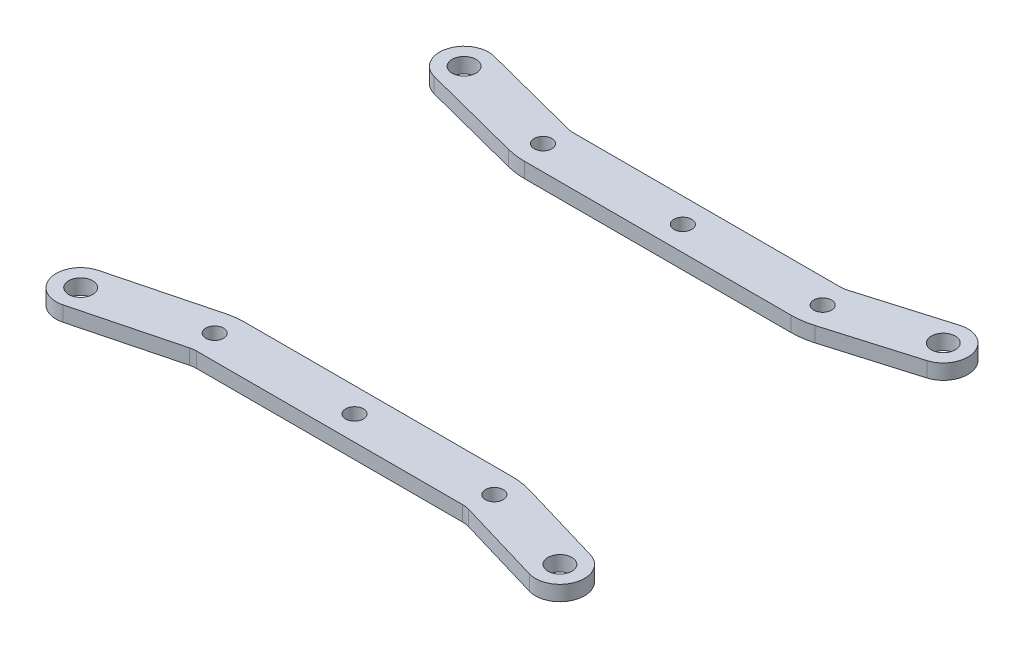
SolidWorks part; units mm, degrees
ref_plane "Front Plane" through (0, 0, 0) normal (0, 0, 1) x (1, 0, 0)
ref_plane "Top Plane" through (0, 0, 0) normal (0, 1, 0) x (1, 0, 0)
ref_plane "Right Plane" through (0, 0, 0) normal (1, 0, 0) x (0, 0, -1)
sketch "Sketch1" plane through (0, 0, 0) normal (0, 1, 0) x (1, 0, 0)
  line L0 (0, 25.4) -> (0, 0) construction
  line L1 (0, 0) -> (25.4, 0) construction
  circle A0 centre (0, 0) radius 3.175
  circle A1 centre (25.4, 0) radius 3.175
  circle A2 centre (50.8, 0) radius 3.175
  circle A3 centre (76.2, 0) radius 3.175
  circle A4 centre (101.6, 0) radius 3.175
  circle A5 centre (127, 0) radius 3.175
  circle A6 centre (152.4, 0) radius 3.175
  circle A7 centre (25.4, 25.4) radius 3.175
  circle A8 centre (50.8, 25.4) radius 3.175
  circle A9 centre (76.2, 25.4) radius 3.175
  circle A10 centre (101.6, 25.4) radius 3.175
  circle A11 centre (127, 25.4) radius 3.175
  circle A12 centre (152.4, 25.4) radius 3.175
  circle A13 centre (25.4, 50.8) radius 3.175
  circle A14 centre (50.8, 50.8) radius 3.175
  circle A15 centre (76.2, 50.8) radius 3.175
  circle A16 centre (101.6, 50.8) radius 3.175
  circle A17 centre (127, 50.8) radius 3.175
  circle A18 centre (152.4, 50.8) radius 3.175
  circle A19 centre (25.4, 76.2) radius 3.175
  circle A20 centre (50.8, 76.2) radius 3.175
  circle A21 centre (76.2, 76.2) radius 3.175
  circle A22 centre (101.6, 76.2) radius 3.175
  circle A23 centre (127, 76.2) radius 3.175
  circle A24 centre (152.4, 76.2) radius 3.175
  circle A25 centre (25.4, 101.6) radius 3.175
  circle A26 centre (50.8, 101.6) radius 3.175
  circle A27 centre (76.2, 101.6) radius 3.175
  circle A28 centre (101.6, 101.6) radius 3.175
  circle A29 centre (127, 101.6) radius 3.175
  circle A30 centre (152.4, 101.6) radius 3.175
  circle A31 centre (25.4, 127) radius 3.175
  circle A32 centre (50.8, 127) radius 3.175
  circle A33 centre (76.2, 127) radius 3.175
  circle A34 centre (101.6, 127) radius 3.175
  circle A35 centre (127, 127) radius 3.175
  circle A36 centre (152.4, 127) radius 3.175
  circle A37 centre (25.4, 152.4) radius 3.175
  circle A38 centre (50.8, 152.4) radius 3.175
  circle A39 centre (76.2, 152.4) radius 3.175
  circle A40 centre (101.6, 152.4) radius 3.175
  circle A41 centre (127, 152.4) radius 3.175
  circle A42 centre (152.4, 152.4) radius 3.175
  circle A43 centre (0, 25.4) radius 3.175
  circle A44 centre (0, 50.8) radius 3.175
  circle A45 centre (0, 76.2) radius 3.175
  circle A46 centre (0, 101.6) radius 3.175
  circle A47 centre (0, 127) radius 3.175
  circle A48 centre (0, 152.4) radius 3.175
  dimension "D1" = 6.35
  dimension "D4" = 25.4
  dimension "D2" = 7
  dimension "D3" = 7
sketch "Sketch2" plane through (0, 0, 0) normal (0, 1, 0) x (1, 0, 0)
  line L0 (25.975, 2.3) -> (25.975, 7.3)
  line L1 (12.925, 99.3) -> (25.975, 99.3)
  line L2 (12.925, 99.3) -> (12.925, 2.3)
  line L3 (12.925, 2.3) -> (25.975, 2.3)
  line L4 (39.975, 99.3) -> (39.975, 2.3)
  line L5 (30.475, 7.3) -> (30.475, 2.3)
  line L6 (25.975, 99.3) -> (25.975, 94.3)
  line L7 (30.475, 94.3) -> (30.475, 99.3)
  line L8 (30.475, 99.3) -> (39.975, 99.3)
  line L9 (30.475, 2.3) -> (39.975, 2.3)
  line L10 (49.975, 99.3) -> (49.975, 2.3)
  line L11 (49.975, 2.3) -> (63.025, 2.3)
  line L12 (63.025, 2.3) -> (63.025, 7.3)
  line L13 (67.525, 7.3) -> (67.525, 2.3)
  line L14 (67.525, 2.3) -> (77.025, 2.3)
  line L15 (77.025, 99.3) -> (77.025, 2.3)
  line L16 (67.525, 99.3) -> (77.025, 99.3)
  line L17 (67.525, 94.3) -> (67.525, 99.3)
  line L18 (63.025, 99.3) -> (63.025, 94.3)
  line L19 (49.975, 99.3) -> (63.025, 99.3)
  line L20 (87.025, 99.3) -> (87.025, 2.3)
  line L21 (87.025, 2.3) -> (100.075, 2.3)
  line L22 (100.075, 2.3) -> (100.075, 7.3)
  line L23 (104.575, 7.3) -> (104.575, 2.3)
  line L24 (104.575, 2.3) -> (114.075, 2.3)
  line L25 (114.075, 99.3) -> (114.075, 2.3)
  line L26 (104.575, 99.3) -> (114.075, 99.3)
  line L27 (104.575, 94.3) -> (104.575, 99.3)
  line L28 (100.075, 99.3) -> (100.075, 94.3)
  line L29 (87.025, 99.3) -> (100.075, 99.3)
  line L30 (12.925, 2.3) -> (114.075, 99.3) construction
  line L31 (0, 101.6) -> (127, 0) construction
  arc A2 (25.975, 7.3) -> (30.475, 7.3) centre (28.225, 7.3) cw
  arc A3 (25.975, 94.3) -> (30.475, 94.3) centre (28.225, 94.3) ccw
  arc A4 (63.025, 7.3) -> (67.525, 7.3) centre (65.275, 7.3) cw
  arc A5 (63.025, 94.3) -> (67.525, 94.3) centre (65.275, 94.3) ccw
  arc A6 (100.075, 7.3) -> (104.575, 7.3) centre (102.325, 7.3) cw
  arc A7 (100.075, 94.3) -> (104.575, 94.3) centre (102.325, 94.3) ccw
  point P44 (63.5, 50.8)
  dimension "D1" = 2.25
  dimension "D2" = 87
  dimension "D3" = 9.5
  dimension "D4" = 97
  dimension "D5" = 13.05
  dimension "D7" = 10
  dimension "D6" = 3
sketch "Sketch3" plane through (0, 0, 0) normal (0, 1, 0) x (1, 0, 0)
  line L0 (-1.6276, 95.3071) -> (24.9962, 88.4212)
  line L1 (29.8789, 87.8) -> (100.4423, 87.8)
  line L2 (105.9743, 88.6011) -> (128.844, 95.367)
  line L3 (1.6276, 107.8929) -> (28.2513, 101.0071)
  line L4 (29.8789, 100.8) -> (100.4423, 100.8)
  line L5 (102.2863, 101.067) -> (125.156, 107.833)
  line L6 (0, 101.6) -> (28.225, 94.3) construction
  line L7 (102.325, 94.3) -> (127, 101.6) construction
  circle A0 centre (28.225, 94.3) radius 2.35
  circle A1 centre (65.275, 94.3) radius 2.35
  circle A2 centre (102.325, 94.3) radius 2.35
  arc A3 (1.6276, 107.8929) -> (-1.6276, 95.3071) centre (0, 101.6) ccw
  arc A4 (128.844, 95.367) -> (125.156, 107.833) centre (127, 101.6) ccw
  arc A5 (24.9962, 88.4212) -> (29.8789, 87.8) centre (29.8789, 107.3) ccw
  arc A6 (100.4423, 87.8) -> (105.9743, 88.6011) centre (100.4423, 107.3) ccw
  arc A7 (28.2513, 101.0071) -> (29.8789, 100.8) centre (29.8789, 107.3) ccw
  arc A8 (100.4423, 100.8) -> (102.2863, 101.067) centre (100.4423, 107.3) ccw
  circle A9 centre (65.275, 94.3) radius 6.5 construction
  circle A10 centre (127, 101.6) radius 3.175
  circle A11 centre (0, 101.6) radius 3.175
  point P30 (0, 0)
  dimension "D1" = 4.7
  dimension "D2" = 6.35
  dimension "D3" = 6.5
extrude "Boss-Extrude1" add sketch "Sketch3" along normal blind 4
ref_plane "Plane1" through (0, 0, -50.8) normal (0, 0, 1) x (1, 0, 0)
mirror "Mirror3" about plane through (0, 0, -50.8) normal (0, 0, 1) of bodies 101
